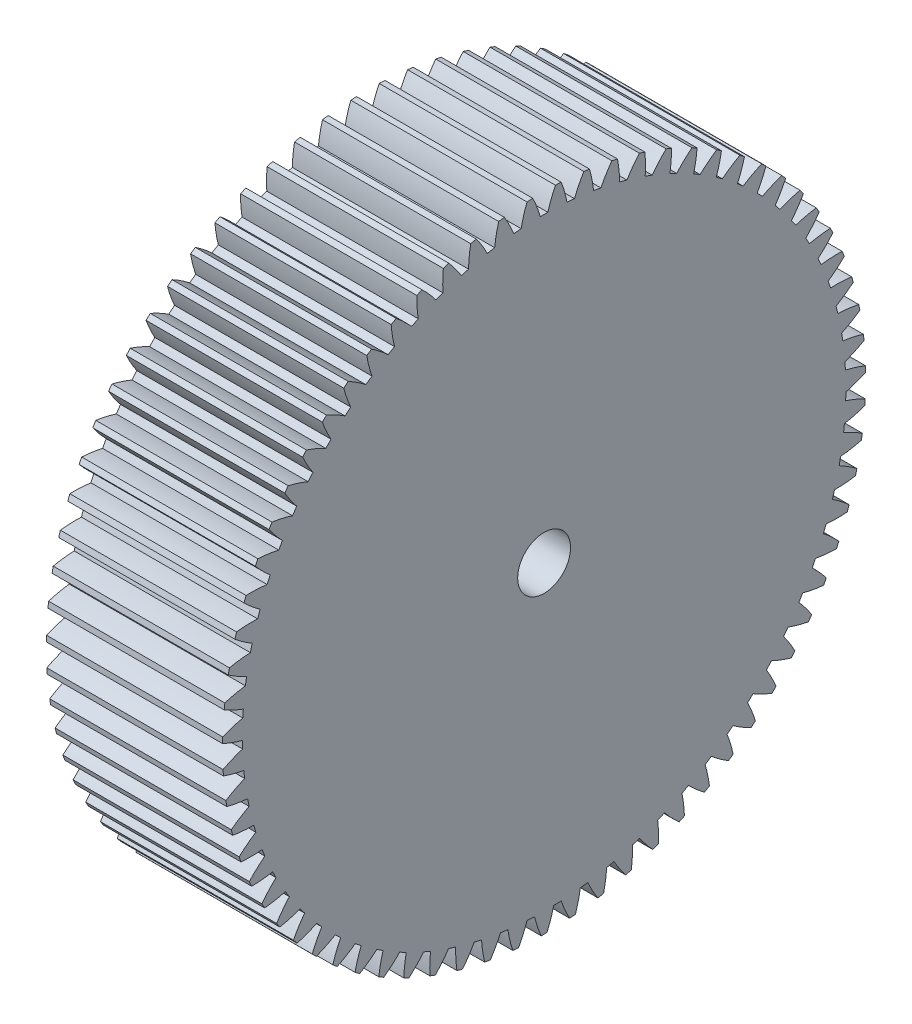
SolidWorks part; units mm, degrees
material "1.0035 (S185)"
ref_plane "Plane1" through (0, 0, 0) normal (0, 0, 1) x (1, 0, 0)
ref_plane "Plane2" through (0, 0, 0) normal (0, 1, 0) x (1, 0, 0)
ref_plane "Plane3" through (0, 0, 0) normal (1, 0, 0) x (0, 0, -1)
sketch "HoldingSke" plane through (0, 0, 0) normal (0, 1, 0) x (1, 0, 0)
  line L0 (0, 0) -> (0.6511, -1.891)
  line L1 (-15, 0) -> (100, 0) construction
  line L2 (0, 0) -> (-2.1039, 2.3779)
  line L3 (0, 0) -> (-11.863, 4.5341)
  line L4 (0, 0) -> (2.8116, 8.1655)
  line L5 (0, 0) -> (-46.8476, -17.4728)
  line L6 (0, 0) -> (-8.2896, -5.593)
  line L7 (-2.1039, 2.3779) -> (8.6586, 51.2059)
  line L8 (-76.2, 54.61) -> (-75.7, 54.61)
  line L9 (-71.009, 38.7566) -> (-53.1078, 45.2721)
  line L10 (-76.2, 71.12) -> (104.1128, 71.12)
  line L11 (0, 0) -> (-10, 0)
  line L12 (-76.2, 101.6) -> (-76.181, 101.6)
  line L13 (24.9733, 27.94) -> (52.9518, 28.4284)
  line L14 (24.9733, 27.94) -> (24.9743, 27.94)
  line L15 (24.9733, 27.94) -> (100.4006, 29.5858)
  line L16 (-63.627, -0.5) -> (-12.827, -0.5)
  circle A0 centre (0, 0) radius 1.5
  circle A1 centre (0, 0) radius 17.124
  circle A2 centre (0, 0) radius 37.5
  circle A3 centre (0, 0) radius 1.5
  dimension "MHD" = 34.248
  dimension "Hub_dia" = 75
  dimension "Bore" = 3
  dimension "MBD" = 3
  dimension "Num_teeth" = 71
  dimension "Pitch_radius" = 180.3128
  dimension "Pitch" = 2
  dimension "Width" = 10
  dimension "Overall_len" = 50
  dimension "Show_teeth" = 71
  dimension "Thickness" = 10
  dimension "OAL" = 50.0001
  dimension "T_dim" = 0.5
  dimension "Ap" = 20
  dimension "H" = 19.05
  dimension "Backlash" = 0.019
  dimension "Addendum_fac" = 1
  dimension "Dedendum_fac" = 1.25
  dimension "Clearance_fac" = 0.25
  dimension "Dedendum_add" = 0.001
  dimension "Module" = 0.5
sketch "BasProSke" plane through (0, 0, 0) normal (0, 1, 0) x (1, 0, 0)
  line L0 (-10, 0) -> (60, 0) construction
  line L1 (0, 0) -> (0, 18.25)
  line L2 (0, 0) -> (10, 0)
  line L3 (10, 0) -> (10, 18.25)
  line L4 (10, 18.25) -> (0, 18.25)
  dimension "Diameter" = 36.5
  dimension "Thickness" = 10
revolve "Base-Revolve" add sketch "BasProSke" angle 360 about L0
sketch "TooCutSke" plane through (0, 0, 0) normal (1, 0, 0) x (0, 0, -1)
  line L1 (0, 0) -> (0, 107) construction
  line L2 (0, 0) -> (-0.4259, 17.7449) construction
  line L3 (0, 0) -> (-1.57, 35.458) construction
  line L4 (-0.4259, 17.7449) -> (-0.785, 17.729) construction
  arc A0 (0.212, 17.1227) -> (-0.212, 17.1227) centre (0, 0) ccw
  arc A1 (0.656, 18.2636) -> (-0.656, 18.2636) centre (0, 0) ccw
  circle A2 centre (0, 0) radius 17.75 construction
  circle A3 centre (0, 0) radius 16.6795 construction
  arc A4 (-0.212, 17.1227) -> (-0.656, 18.2636) centre (-7.0259, 15.1276) ccw
  arc A5 (0.656, 18.2636) -> (0.212, 17.1227) centre (7.0259, 15.1276) ccw
  dimension "Root_dia" = 34.248
  dimension "Overcut_dia" = 36.5508
  dimension "Pitch_dia" = 35.5
  dimension "Base_dia" = 33.3591
  dimension "Flank_rad" = 7.1
  dimension "Half_ang" = 2.535
  dimension "Half_CT" = 0.3594
extrude "ToothCut" cut sketch "TooCutSke" along normal through all
fillet "Breaks" [suppressed] radius 0.01
fillet "RootFillets" [suppressed] radius 0.126
pattern_circular "TeethCuts" count 71 every 5.07 about axis through (-10, 0, 0) along (1, 0, 0) of "ToothCut", "RootFillets", "Breaks"
sketch "HubNeaOneSke" plane through (0, 0, 0) normal (-1, 0, 0) x (0, 0, 1)
  circle A0 centre (0, 0) radius 17.124
  dimension "Diameter" = 34.248
extrude "HubNearOne" [suppressed] add sketch "HubNeaOneSke" along normal blind 40.0001
sketch "HubNeaBotSke" plane through (0, 0, 0) normal (-1, 0, 0) x (0, 0, 1)
  circle A0 centre (0, 0) radius 17.124
  dimension "Diameter" = 34.248
extrude "HubNearBoth" [suppressed] add sketch "HubNeaBotSke" along normal blind 20
ref_plane "FarPln" through (10, 0, 0) normal (1, 0, 0) x (0, 0, -1)
sketch "HubFarSke" plane through (10, 0, 0) normal (1, 0, 0) x (0, 0, -1)
  circle A0 centre (0, 0) radius 17.124
  dimension "Diameter" = 34.248
extrude "HubFar" [suppressed] add sketch "HubFarSke" along normal blind 20
sketch "BorSke" plane through (0, 0, 0) normal (1, 0, 0) x (0, 0, -1)
  circle A0 centre (0, 0) radius 1.5
  dimension "Diameter" = 3
extrude "Bore" cut sketch "BorSke" along normal mid plane 100.0001
sketch "KeySke" plane through (0, 0, 0) normal (1, 0, 0) x (0, 0, -1)
  line L0 (-0.6, 0) -> (-0.6, 2)
  line L1 (-0.6, 2) -> (0.6, 2)
  line L2 (0.6, 2) -> (0.6, 0)
  line L3 (0, 0) -> (0, 34) construction
  line L4 (-0.6, 0) -> (0.6, 0)
  dimension "Offset" = 2
  dimension "Width" = 1.2
extrude "Keyway" [suppressed] cut sketch "KeySke" along normal mid plane 100.0001
pattern_circular "Keyway2" [suppressed] count 2 every 90 about axis through (-10, 0, 0) along (1, 0, 0)
equation "' \"Module@HoldingSke\" = 6.35"
equation "' \"Num_teeth@HoldingSke\" = 12"
equation "' \"Ap@HoldingSke\" =  20"
equation "' \"Width@HoldingSke\" = 0.5 * 25.4"
equation "' \"Hub_dia@HoldingSke\"= 1 * 25.4"
equation "' \"Overall_len@HoldingSke\" = 1.0 * 25.4"
equation "' \"Bore@HoldingSke\" = 0.75 * 25.4"
equation "' \"T_dim@HoldingSke\" = 0.1 * 25.4"
equation "' \"Width@KeySke\" = 0.25 * 25.4"
equation "' \"Show_teeth@HoldingSke\" = 13"
equation "' \"Backlash@HoldingSke\" = 0.009 * 25.4"
equation "' \"Addendum_fac@HoldingSke\" = 1.0"
equation "' \"Dedendum_fac@HoldingSke\" = 1.25"
equation "' \"Dedendum_add@HoldingSke\" = 0.00005 * 25.4"
equation "' \"Clearance_fac@HoldingSke\" = 0.25"
equation "\"Pitch@HoldingSke\" = 1 / \"Module@HoldingSke\""
equation "\"Overcut_dia@TooCutSke\" = (\"Num_teeth@HoldingSke\" + 2 * \"Addendum_fac@HoldingSke\") / \"Pitch@HoldingSke\" + 0.002 * 25.4"
equation "\"Pitch_dia@TooCutSke\" = \"Num_teeth@HoldingSke\" / \"Pitch@HoldingSke\""
equation "\"Base_dia@TooCutSke\" = \"Num_teeth@HoldingSke\" / \"Pitch@HoldingSke\" * cos((\"Ap@HoldingSke\"  * 3.14159265 / 180))"
equation "\"Root_dia@TooCutSke\" = (\"Num_teeth@HoldingSke\" + 2) / \"Pitch@HoldingSke\" - 2 * (\"Addendum_fac@HoldingSke\" + \"Dedendum_fac@HoldingSke\") / \"Pitch@HoldingSke\" - \"Dedendum_add@HoldingSke\" * 2"
equation "\"Half_ang@TooCutSke\" = 180 / \"Num_teeth@HoldingSke\""
equation "\"Half_CT@TooCutSke\" = \"Num_teeth@HoldingSke\" / \"Pitch@HoldingSke\" * sin((3.14159265 / 2 / \"Num_teeth@HoldingSke\")) / 2 - 7 * \"Backlash@HoldingSke\" / 4"
equation "\"Flank_rad@TooCutSke\" = \"Num_teeth@HoldingSke\" / \"Pitch@HoldingSke\" / 5"
equation "\"Radius@RootFillets\" = \"Clearance_fac@HoldingSke\" / \"Pitch@HoldingSke\" + \"Dedendum_add@HoldingSke\""
equation "\"Break_rad@Breaks\" = 0.02 / \"Pitch@HoldingSke\""
equation "\"Thickness@HoldingSke\" = \"Width@HoldingSke\""
equation "\"OAL@HoldingSke\" = \"Thickness@HoldingSke\""
equation "\"MHD@HoldingSke\" = (\"Num_teeth@HoldingSke\" + 2) / \"Pitch@HoldingSke\" - 2 * (\"Addendum_fac@HoldingSke\" + \"Dedendum_fac@HoldingSke\")  / \"Pitch@HoldingSke\" - \"Dedendum_add@HoldingSke\" * 2"
equation "\"MBD@HoldingSke\" = (\"Num_teeth@HoldingSke\" + 2) / \"Pitch@HoldingSke\" - 2 * (\"Addendum_fac@HoldingSke\" + \"Dedendum_fac@HoldingSke\")  / \"Pitch@HoldingSke\" - \"Dedendum_add@HoldingSke\" * 2 - 0.002 * 25.4"
equation "\"MHD@HoldingSke\" = ((sgn( \"MHD@HoldingSke\" - \"Hub_dia@HoldingSke\" )-1)*( \"MHD@HoldingSke\" - \"Hub_dia@HoldingSke\" ))/-2+ \"Hub_dia@HoldingSke\""
equation "\"MBD@HoldingSke\" = ((sgn( \"MBD@HoldingSke\" - \"Bore@HoldingSke\" )-1)*( \"MBD@HoldingSke\" - \"Bore@HoldingSke\" ))/-2+ \"Bore@HoldingSke\""
equation "\"OAL@HoldingSke\" = ((sgn( \"OAL@HoldingSke\" - \"Overall_len@HoldingSke\" )+1)*( \"OAL@HoldingSke\" - \"Overall_len@HoldingSke\" ))/2 + \"Overall_len@HoldingSke\" + 0.000002 * 25.4"
equation "\"Num_teeth@TeethCuts\" = int( \"Show_teeth@HoldingSke\" ) + 1"
equation "\"Num_teeth@TeethCuts\" = ((sgn( \"Num_teeth@TeethCuts\" - \"Num_teeth@HoldingSke\" )-1)*( \"Num_teeth@TeethCuts\" - \"Num_teeth@HoldingSke\" ))/-2+ \"Num_teeth@HoldingSke\""
equation "\"Num_teeth@TeethCuts\" = ((sgn( \"Num_teeth@TeethCuts\" - 2.0)+1)*( \"Num_teeth@TeethCuts\" - 2.0))/2 +2.0"
equation "\"Angle@TeethCuts\" = 360.0 / \"Num_teeth@HoldingSke\""
equation "\"Diameter@BasProSke\" = (\"Num_teeth@HoldingSke\" + 2 * \"Addendum_fac@HoldingSke\") / \"Pitch@HoldingSke\""
equation "\"Thickness@BasProSke\"  = \"Thickness@HoldingSke\""
equation "' \"Fillet_rad@BasProSke\" =  \"Thickness@HoldingSke\" * 0.05"
equation "\"MHD@HoldingSke\" = ((sgn( \"MHD@HoldingSke\" - \"Root_dia@TooCutSke\" )-1)*( \"MHD@HoldingSke\" - \"Root_dia@TooCutSke\" ))/-2+ \"Root_dia@TooCutSke\""
equation "\"Diameter@HubNeaOneSke\" = \"MHD@HoldingSke\""
equation "\"Length@HubNearOne\" = \"OAL@HoldingSke\" - \"Thickness@BasProSke\""
equation "\"Diameter@HubNeaBotSke\" = \"MHD@HoldingSke\""
equation "\"Length@HubNearBoth\" = ( \"OAL@HoldingSke\" - \"Thickness@BasProSke\" ) / 2.0"
equation "\"Thickness@FarPln\" = \"Thickness@BasProSke\""
equation "\"Diameter@HubFarSke\" = \"MHD@HoldingSke\""
equation "\"Length@HubFar\" = ( \"OAL@HoldingSke\" - \"Thickness@BasProSke\" ) / 2.0"
equation "\"Diameter@BorSke\" = \"MBD@HoldingSke\""
equation "\"D1@Bore\" = \"OAL@HoldingSke\" * 2.0"
equation "\"D1@Keyway\" = \"OAL@HoldingSke\" * 2.0"
equation "\"Offset@KeySke\" = \"T_dim@HoldingSke\" + \"MBD@HoldingSke\" / 2.0"
